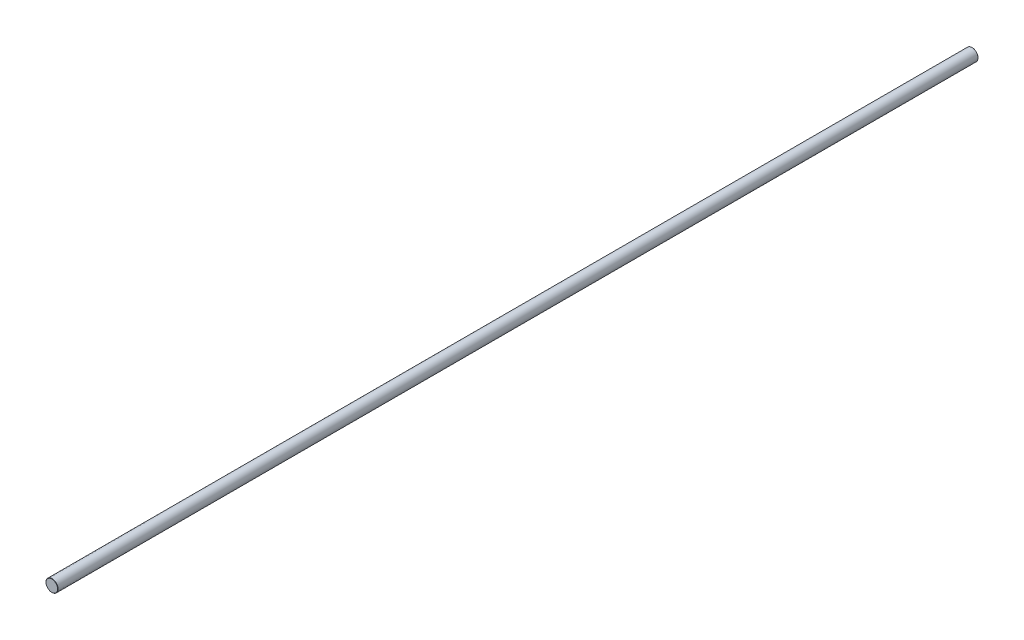
SolidWorks part; units mm, degrees
material "AISI 1045 Steel, cold drawn"
ref_plane "Front Plane" through (0, 0, 0) normal (0, 0, 1) x (1, 0, 0)
ref_plane "Top Plane" through (0, 0, 0) normal (0, 1, 0) x (1, 0, 0)
ref_plane "Right Plane" through (0, 0, 0) normal (1, 0, 0) x (0, 0, -1)
sketch "Sketch1" plane through (0, 0, 0) normal (0, 0, 1) x (1, 0, 0)
  circle A0 centre (0, 0) radius 6 construction
  dimension "Diameter" = 12
sketch "Sketch2" plane through (0, 0, 0) normal (1, 0, 0) x (0, 0, -1)
  line L0 (457.5, 0) -> (-457.5, 0) construction
  point P0 (-366, 0)
  point P3 (0, 0)
  point P4 (366, 0)
  point P6 (-320.25, 0)
  point P7 (320.25, 0)
  dimension "Length" = 915
  dimension "D1" = 91.5
  dimension "D2" = 91.5
  dimension "D3" = 137.25
  dimension "D4" = 137.25
sketch "Sketch3" plane through (0, 0, 0) normal (0, 0, 1) x (1, 0, 0)
  circle A0 centre (0, 0) radius 6 construction
  circle A1 centre (0, 0) radius 6
extrude "Boss-Extrude1" add sketch "Sketch3" along normal up to vertex (457.5 mm away) and the other way up to vertex (457.5 mm away) up to point (0, 0, 457.5) other way up to point (0, 0, -457.5)
chamfer "Chamfer1" distance 0.24 angle 45 2 edges at (6, 0, 457.5) (6, 0, -457.5)
equation "\"D1@Chamfer1\"=\"Diameter@Sketch1\"*.02"
equation "\"D1@Sketch2\"=\"D2@Sketch2\""
equation "\"D2@Sketch2\"=\"Length@Sketch2\"*.1"
equation "\"D3@Sketch2\"=\"Length@Sketch2\"*.15"
equation "\"D4@Sketch2\"=\"D3@Sketch2\""
